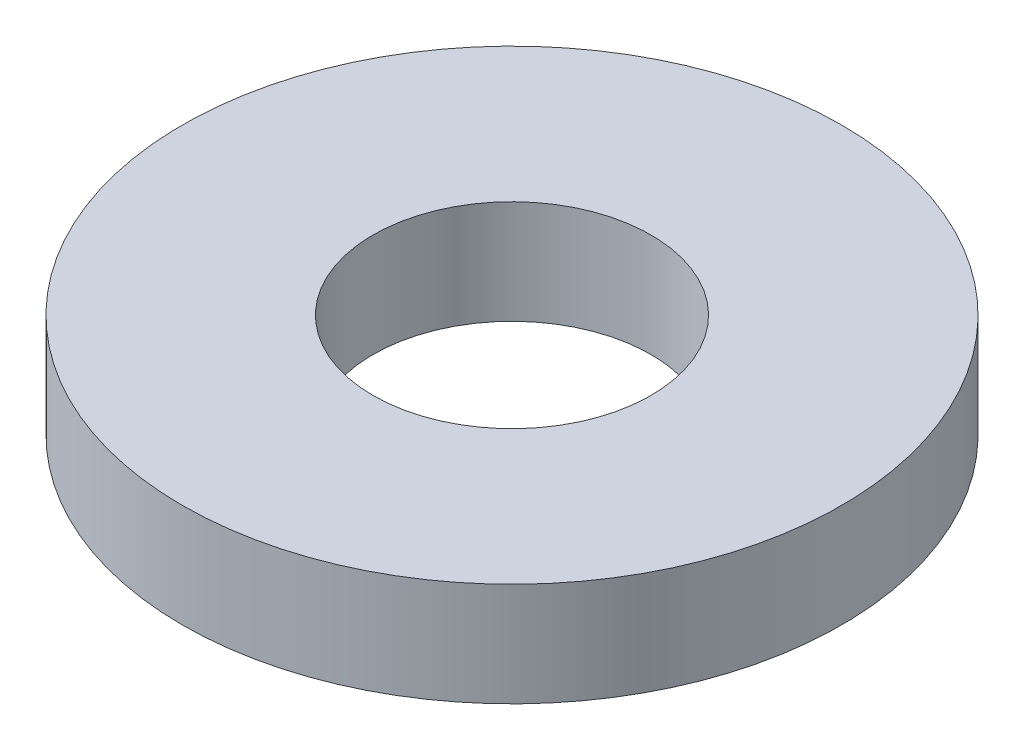
SolidWorks part; units mm, degrees
ref_plane "Front Plane" through (0, 0, 0) normal (0, 0, 1) x (1, 0, 0)
ref_plane "Top Plane" through (0, 0, 0) normal (0, 1, 0) x (1, 0, 0)
ref_plane "Right Plane" through (0, 0, 0) normal (1, 0, 0) x (0, 0, -1)
sketch "Sketch1" plane through (0, 0, 0) normal (0, 1, 0) x (1, 0, 0)
  circle A0 centre (0, 0) radius 17.78
  circle A1 centre (0, 0) radius 7.5
  dimension "D1" = 35.56
  dimension "D2" = 15
extrude "Boss-Extrude1" add sketch "Sketch1" along normal blind 5.588
